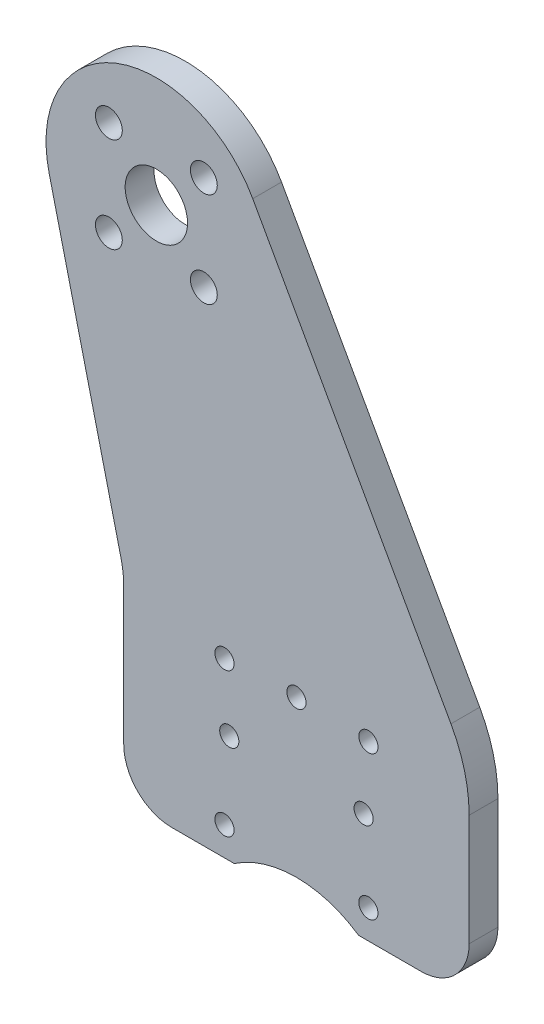
SolidWorks part; units mm, degrees
ref_plane "Спереди" through (0, 0, 0) normal (0, 0, 1) x (1, 0, 0)
ref_plane "Сверху" through (0, 0, 0) normal (0, 1, 0) x (1, 0, 0)
ref_plane "Справа" through (0, 0, 0) normal (1, 0, 0) x (0, 0, -1)
sketch "Эскиз1" plane through (0, 0, 0) normal (0, 0, 1) x (1, 0, 0)
  line L0 (0, 0) -> (0, -64.8775) construction
  line L1 (-4.9497, 4.9497) -> (4.9497, 4.9497) construction
  line L2 (-4.9497, 4.9497) -> (-4.9497, -4.9497) construction
  line L3 (-4.9497, -4.9497) -> (4.9497, -4.9497) construction
  line L4 (4.9497, 4.9497) -> (4.9497, -4.9497) construction
  line L5 (-4.9497, 4.9497) -> (4.9497, -4.9497) construction
  line L6 (-4.9497, -4.9497) -> (4.9497, 4.9497) construction
  line L7 (0, -64.8775) -> (14.6, -64.8775) construction
  line L8 (24.6, -34.8775) -> (4.6, -34.8775) construction
  line L9 (24.6, -34.8775) -> (24.6, -74.8775) construction
  line L10 (4.6, -34.8775) -> (4.6, -74.8775) construction
  line L11 (4.6, -74.8775) -> (24.6, -74.8775) construction
  line L12 (1.6, -55.3775) -> (8.1193, -55.3775)
  line L13 (21.0807, -55.3775) -> (27.6, -55.3775)
  line L14 (-3.4, -36.069) -> (-3.4, -50.3775)
  line L15 (-3.68, -33.7193) -> (-11.178, -2.7022)
  line L16 (32.6, -38.7747) -> (32.6, -50.3775)
  line L17 (30.703, -31.4732) -> (10.0456, 5.5978)
  circle A0 centre (0, 0) radius 3.25
  circle A1 centre (-4.9497, 4.9497) radius 1.4
  circle A2 centre (4.9497, 4.9497) radius 1.4
  circle A3 centre (4.9497, -4.9497) radius 1.4
  circle A4 centre (-4.9497, -4.9497) radius 1.4
  circle A5 centre (0, 0) radius 10 construction
  circle A6 centre (7.1, -37.3775) radius 1
  circle A7 centre (22.1, -37.3775) radius 1
  circle A8 centre (7.1, -52.3775) radius 1
  circle A9 centre (22.1, -52.3775) radius 1
  arc A10 (10.0456, 5.5978) -> (-11.178, -2.7022) centre (0, 0) ccw
  circle A11 centre (14.6, -64.8775) radius 10 construction
  circle A12 centre (14.6, -37.1275) radius 1
  circle A13 centre (21.6, -44.1275) radius 1
  circle A14 centre (7.6, -44.1275) radius 1
  arc A15 (21.0807, -55.3775) -> (8.1193, -55.3775) centre (14.6, -64.8775) ccw
  arc A16 (32.6, -50.3775) -> (27.6, -55.3775) centre (27.6, -50.3775) cw
  arc A17 (1.6, -55.3775) -> (-3.4, -50.3775) centre (1.6, -50.3775) cw
  arc A18 (32.6, -38.7747) -> (30.703, -31.4732) centre (17.6, -38.7747) ccw
  arc A19 (-3.4, -36.069) -> (-3.68, -33.7193) centre (-13.4, -36.069) ccw
  point P3 (0, 0)
  point P47 (-3.4, -55.3775)
  point P50 (32.6, -34.8775)
  point P53 (-3.4, -34.8775)
  point P55 (14.0693, -37.9751)
  dimension "D1" = 6.5
  dimension "D3" = 2.8
  dimension "D6" = 20
  dimension "D9" = 2
  dimension "D15" = 23
  dimension "D16" = 10
  dimension "D17" = 23
  dimension "D21" = 5
  dimension "D22" = 15
  dimension "D23" = 10
  dimension "D2" = 14
  dimension "D4" = 66.5
  dimension "D5" = 14.6
  dimension "D7" = 27.5
  dimension "D8" = 7.5
  dimension "D10" = 15
  dimension "D11" = 15
  dimension "D12" = 30
  dimension "D13" = 20
  dimension "D14" = 40
  dimension "D18" = 3
  dimension "D19" = 7
  dimension "D20" = 8
  dimension "D24" = 27.75
  dimension "D25" = 7
  dimension "D26" = 7
extrude "Бобышка-Вытянуть1" add sketch "Эскиз1" against normal blind 3
